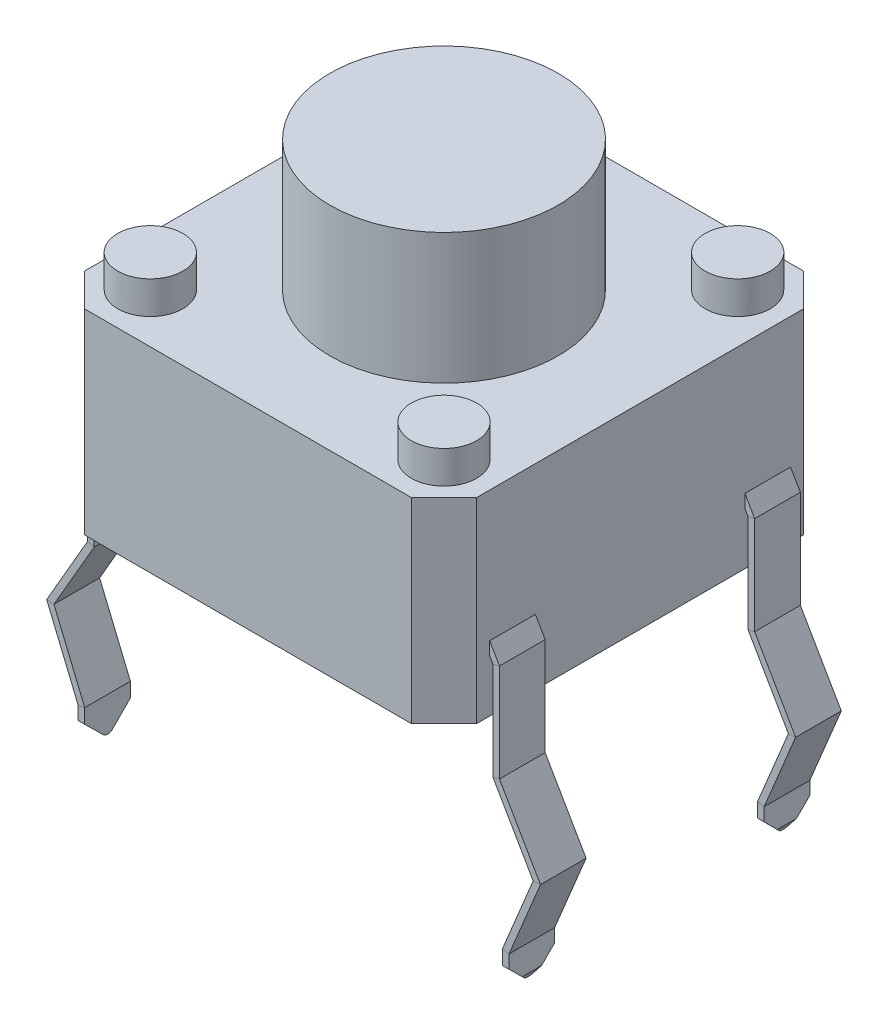
SolidWorks part; units mm, degrees
ref_plane "Front Plane" through (0, 0, 0) normal (0, 0, 1) x (1, 0, 0)
ref_plane "Top Plane" through (0, 0, 0) normal (0, 1, 0) x (1, 0, 0)
ref_plane "Right Plane" through (0, 0, 0) normal (1, 0, 0) x (0, 0, -1)
sketch "Sketch1" plane through (0, 0, 0) normal (0, 1, 0) x (1, 0, 0)
  line L1 (-3.005, -3.005) -> (3.005, -3.005)
  line L2 (-3.005, -3.005) -> (-3.005, 3.005)
  line L3 (-3.005, 3.005) -> (3.005, 3.005)
  line L4 (3.005, -3.005) -> (3.005, 3.005)
  line L5 (-3.005, -3.005) -> (3.005, 3.005) construction
  line L6 (-3.005, 3.005) -> (3.005, -3.005) construction
  point P0 (0, 0)
  dimension "D1" = 6.01
  dimension "D2" = 6.01
extrude "Boss-Extrude1" add sketch "Sketch1" along normal blind 3
chamfer "Chamfer1" distance 0.5 angle 45 4 edges at (3.005, 1.5, -3.005) (-3.005, 1.5, -3.005) (-3.005, 1.5, 3.005) (3.005, 1.5, 3.005)
sketch "Sketch3" plane through (0, 3, 0) normal (0, 1, 0) x (1, 0, 0)
  circle A0 centre (0, 0) radius 1.75
extrude "Boss-Extrude2" add sketch "Sketch3" along normal blind 2
sketch "Sketch4" plane through (0, 3, 0) normal (0, 1, 0) x (1, 0, 0)
  circle A0 centre (2.25, 2.25) radius 0.5
  circle A1 centre (2.25, -2.25) radius 0.5
  circle A2 centre (-2.25, 2.25) radius 0.5
sketch "Sketch5" plane through (0, 3, 0) normal (0, 1, 0) x (1, 0, 0)
  circle A0 centre (-2.25, -2.25) radius 0.5
extrude "Boss-Extrude6" add sketch "Sketch4" along normal blind 0.5
extrude "Boss-Extrude7" add sketch "Sketch5" along normal blind 0.5
sketch "Sketch6" plane through (-3.005, 0, 0) normal (-1, 0, 0) x (0, 0, 1)
  line L0 (-2.505, 0) -> (2.505, 0) construction
  line L1 (-2.305, 1) -> (-1.605, 1)
  line L2 (-2.305, 1) -> (-2.305, 0.8)
  line L3 (-2.305, 0.8) -> (-1.605, 0.8)
  line L4 (-1.605, 1) -> (-1.605, 0.8)
  line L5 (-2.305, 1) -> (-1.605, 0.8) construction
  line L6 (-2.305, 0.8) -> (-1.605, 1) construction
  line L7 (-2.505, 3) -> (-2.505, 0) construction
  point P0 (-1.955, 0.9)
  dimension "D1" = 0.7
  dimension "D2" = 0.2
  dimension "D3" = 1
  dimension "D4" = 0.2
sketch "Sketch7" plane through (0, 0, 0) normal (0, 0, 1) x (1, 0, 0)
  line L0 (-3.005, 0.9) -> (-3.105, 0.7268)
  line L1 (-3.105, 0.7268) -> (-3.105, -0.7732)
  line L2 (-3.105, -0.7732) -> (-3.7272, -1.8508)
  line L3 (-3.7272, -1.8508) -> (-3.25, -3)
  line L4 (-3.25, -3) -> (-3.25, -3.5)
  line L5 (2.505, 0) -> (-2.505, 0) construction
  line L6 (-3.005, 3) -> (-3.005, 0) construction
  dimension "D1" = 3.5
  dimension "D2" = 0.1
  dimension "D3" = 3.25
  dimension "D4" = 0.5
  dimension "D5" = 1.5
  dimension "D6" = 150
  dimension "D7" = 150
sweep "Sweep1" add profiles "Sketch6" path "Sketch7"
mirror "Mirror1" about plane through (0, 0, 0) normal (0, 0, 1) of "Sweep1"
mirror "Mirror2" about plane through (0, 0, 0) normal (1, 0, 0) of "Mirror1", "Sweep1"
sketch "Sketch8" plane through (0, 0, 0) normal (1, 0, 0) x (0, 0, -1)
  line L0 (-2.305, -3.2117) -> (-2.305, -3.5866)
  line L1 (-2.305, -3.01) -> (-2.305, -3.4134) construction
  line L2 (-2.305, -3.5866) -> (-1.605, -3.5866)
  line L3 (-1.605, -3.5866) -> (-1.605, -3.2117)
  line L4 (-1.605, -3.01) -> (-1.605, -3.4134) construction
  line L5 (-1.605, -3.2117) -> (-1.8817, -3.4893)
  line L6 (-2.0227, -3.4899) -> (-2.305, -3.2117)
  arc A0 (-1.8817, -3.4893) -> (-2.0227, -3.4899) centre (-1.9525, -3.4187) cw
  dimension "D1" = 0.1
extrude "Cut-Extrude1" cut sketch "Sketch8" against normal through all and the other way through all
mirror "Mirror3" about plane through (0, 0, 0) normal (0, 0, 1) of "Cut-Extrude1"
